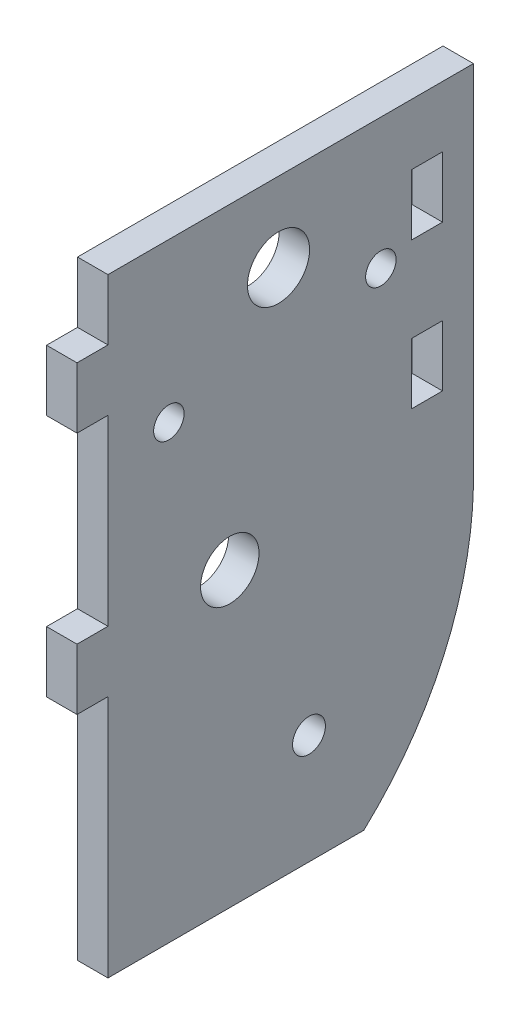
SolidWorks part; units mm, degrees
ref_plane "Front Plane" through (0, 0, 0) normal (0, 0, 1) x (1, 0, 0)
ref_plane "Top Plane" through (0, 0, 0) normal (0, 1, 0) x (1, 0, 0)
ref_plane "Right Plane" through (0, 0, 0) normal (1, 0, 0) x (0, 0, -1)
sketch "Sketch1" plane through (0, 0, 0) normal (1, 0, 0) x (0, 0, -1)
  line L1 (-19.05, -31.75) -> (19.05, -31.75)
  line L2 (-19.05, -31.75) -> (-19.05, 31.75)
  line L3 (-19.05, 31.75) -> (19.05, 31.75)
  line L4 (19.05, -31.75) -> (19.05, 31.75)
  line L5 (-19.05, -31.75) -> (19.05, 31.75) construction
  line L6 (-19.05, 31.75) -> (19.05, -31.75) construction
  point P0 (0, 0)
  dimension "D1" = 63.5
  dimension "D2" = 38.1
extrude "main body" add sketch "Sketch1" along normal blind 3.175
sketch "Sketch2" plane through (3.175, 0, 0) normal (1, 0, 0) x (0, 0, -1)
  line L0 (-19.05, 25.4) -> (-22.2758, 25.4)
  line L1 (-19.05, 31.75) -> (-19.05, -31.75) construction
  line L2 (-22.2758, 25.4) -> (-22.2758, 19.05)
  line L3 (-22.2758, 19.05) -> (-19.05, 19.05)
  line L4 (-19.05, 19.05) -> (-19.05, 25.4)
  line L5 (19.05, 31.75) -> (-19.05, 31.75) construction
  line L6 (-19.05, -6.35) -> (-22.2758, -6.35)
  line L7 (-22.2758, -6.35) -> (-22.2758, 0)
  line L8 (-22.2758, 0) -> (-19.05, 0)
  line L9 (-19.05, 0) -> (-19.05, -6.35)
  dimension "D1" = 3.2258
  dimension "D2" = 6.35
  dimension "D3" = 6.35
  dimension "D4" = 3.2258
  dimension "D5" = 6.35
  dimension "D6" = 19.05
extrude "tabs" add sketch "Sketch2" against normal blind 3.175
sketch "Sketch5" plane through (3.175, 0, 0) normal (1, 0, 0) x (0, 0, -1)
  line L4 (-19.05, -31.75) -> (19.05, -31.75) construction
  line L5 (-19.05, -6.35) -> (-19.05, -31.75) construction
  circle A0 centre (1.905, -20.32) radius 1.7145
  dimension "D3" = 3.429
  dimension "D1" = 20.955
  dimension "D2" = 11.43
extrude "motor cut" cut sketch "Sketch5" against normal through all
sketch "Sketch6" plane through (3.175, 0, 0) normal (1, 0, 0) x (0, 0, -1)
  line L0 (-19.05, 31.75) -> (-19.05, 25.4) construction
  line L1 (19.05, 31.75) -> (-19.05, 31.75) construction
  circle A0 centre (-1.27, 23.495) radius 3.2385
  dimension "D3" = 6.477
  dimension "D1" = 17.78
  dimension "D2" = 8.255
extrude "cut for axle" cut sketch "Sketch6" against normal through all
sketch "Sketch7" plane through (3.175, 0, 0) normal (1, 0, 0) x (0, 0, -1)
  line L0 (19.05, -31.75) -> (19.05, -6.35)
  line L1 (19.05, -31.75) -> (19.05, 31.75) construction
  line L2 (19.05, -31.75) -> (7.62, -31.75)
  line L3 (-19.05, -31.75) -> (19.05, -31.75) construction
  arc A0 (19.05, -6.35) -> (7.62, -31.75) centre (-16.5026, -5.6231) cw
  dimension "D1" = 25.4
  dimension "D2" = 11.43
extrude "round off back corner" cut sketch "Sketch7" against normal through all
sketch "Sketch9" plane through (3.175, 0, 0) normal (1, 0, 0) x (0, 0, -1)
  line L0 (14.2113, 22.225) -> (14.2113, 6.985) construction
  line L1 (12.5984, 25.4) -> (15.8242, 25.4)
  line L2 (12.5984, 25.4) -> (12.5984, 19.05)
  line L3 (12.5984, 19.05) -> (15.8242, 19.05)
  line L4 (15.8242, 25.4) -> (15.8242, 19.05)
  line L5 (12.5984, 25.4) -> (15.8242, 19.05) construction
  line L6 (12.5984, 19.05) -> (15.8242, 25.4) construction
  line L7 (12.5984, 10.16) -> (15.8242, 10.16)
  line L8 (12.5984, 10.16) -> (12.5984, 3.81)
  line L9 (12.5984, 3.81) -> (15.8242, 3.81)
  line L10 (15.8242, 10.16) -> (15.8242, 3.81)
  line L11 (12.5984, 10.16) -> (15.8242, 3.81) construction
  line L12 (12.5984, 3.81) -> (15.8242, 10.16) construction
  line L13 (19.05, -6.35) -> (19.05, 31.75) construction
  line L14 (19.05, 31.75) -> (-19.05, 31.75) construction
  point P0 (14.2113, 22.225)
  point P5 (14.2113, 6.985)
  dimension "D1" = 8.89
  dimension "D2" = 6.35
  dimension "D3" = 3.2258
  dimension "D4" = 3.2258
  dimension "D5" = 6.35
  dimension "D6" = 3.2258
  dimension "D7" = 6.35
extrude "cut for tabs" cut sketch "Sketch9" against normal through all
sketch "Sketch10" plane through (0, 0, 0) normal (-1, 0, 0) x (0, 0, 1)
  line L1 (19.05, -31.75) -> (-7.62, -31.75) construction
  line L2 (19.05, 19.05) -> (19.05, 0) construction
  circle A0 centre (6.35, -1.27) radius 3.048
  dimension "D1" = 6.096
  dimension "D2" = 12.7
  dimension "D3" = 30.48
extrude "cut for screw access" cut sketch "Sketch10" against normal through all
sketch "Sketch11" plane through (0, 0, 0) normal (-1, 0, 0) x (0, 0, 1)
  line L0 (-19.05, 31.75) -> (19.05, 31.75) construction
  line L1 (19.05, 19.05) -> (19.05, 0) construction
  circle A0 centre (12.7, 15.24) radius 1.5875
  dimension "D1" = 3.175
  dimension "D2" = 16.51
  dimension "D3" = 6.35
extrude "cut for bracket screw" cut sketch "Sketch11" against normal through all
sketch "Sketch12" plane through (0, 0, 0) normal (-1, 0, 0) x (0, 0, 1)
  circle A0 centre (-9.398, 18.0975) radius 1.5875
  circle A1 centre (1.27, 23.495) radius 3.2385 construction
  dimension "D1" = 3.175
  dimension "D2" = 10.668
  dimension "D3" = 5.3975
extrude "cut for basic tilt lock screw" cut sketch "Sketch12" against normal through all
